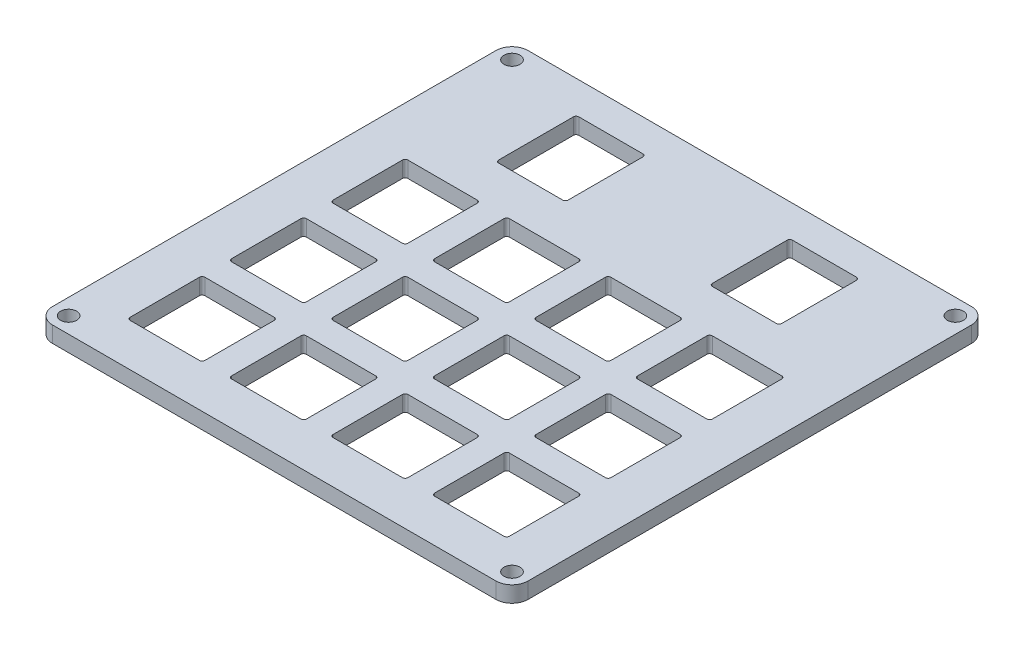
SolidWorks part; units mm, degrees
ref_plane "Front Plane" through (0, 0, 0) normal (0, 0, 1) x (1, 0, 0)
ref_plane "Top Plane" through (0, 0, 0) normal (0, 1, 0) x (1, 0, 0)
ref_plane "Right Plane" through (0, 0, 0) normal (1, 0, 0) x (0, 0, -1)
sketch "Sketch1" plane through (0, 0, 0) normal (0, 1, 0) x (1, 0, 0)
  line L0 (0, 0) -> (0, 50000) construction
  line L1 (-41.5, -44.5) -> (41.5, -44.5)
  line L3 (-41.5, 44.5) -> (41.5, 44.5)
  line L4 (44.5, -41.5) -> (44.5, 41.5)
  line L5 (-44.5, -44.5) -> (44.5, 44.5) construction
  line L6 (-44.5, 44.5) -> (44.5, -44.5) construction
  line L7 (0, 0) -> (50000, 0) construction
  line L19 (26, 23.5) -> (14, 23.5)
  line L20 (-29.9303, 29.9303) -> (38.5, -38.5) construction
  line L26 (-44.5, -41.5) -> (-44.5, 41.5)
  line L32 (-16.5, -36) -> (-16.5, -23)
  line L33 (-35, -36.5) -> (-22, -36.5)
  line L34 (-35.5, -36) -> (-35.5, -23)
  line L35 (-35, -22.5) -> (-22, -22.5)
  line L36 (-21.5, -36) -> (-21.5, -23)
  line L37 (-16, -36.5) -> (-3, -36.5)
  line L38 (-2.5, -36) -> (-2.5, -23)
  line L39 (-16, -22.5) -> (-3, -22.5)
  line L40 (2.5, -36) -> (2.5, -23)
  line L41 (3, -36.5) -> (16, -36.5)
  line L42 (16.5, -36) -> (16.5, -23)
  line L43 (3, -22.5) -> (16, -22.5)
  line L44 (21.5, -36) -> (21.5, -23)
  line L45 (22, -36.5) -> (35, -36.5)
  line L46 (35.5, -36) -> (35.5, -23)
  line L47 (22, -22.5) -> (35, -22.5)
  line L48 (-16.5, -17) -> (-16.5, -4)
  line L49 (-16, -17.5) -> (-3, -17.5)
  line L50 (-2.5, -17) -> (-2.5, -4)
  line L51 (-16, -3.5) -> (-3, -3.5)
  line L52 (2.5, -17) -> (2.5, -4)
  line L53 (3, -17.5) -> (16, -17.5)
  line L54 (16.5, -17) -> (16.5, -4)
  line L55 (3, -3.5) -> (16, -3.5)
  line L56 (21.5, -17) -> (21.5, -4)
  line L57 (22, -17.5) -> (35, -17.5)
  line L58 (35.5, -17) -> (35.5, -4)
  line L59 (22, -3.5) -> (35, -3.5)
  line L60 (-16.5, 2) -> (-16.5, 15)
  line L61 (-16, 1.5) -> (-3, 1.5)
  line L62 (-2.5, 2) -> (-2.5, 15)
  line L63 (-16, 15.5) -> (-3, 15.5)
  line L64 (2.5, 2) -> (2.5, 15)
  line L65 (3, 1.5) -> (16, 1.5)
  line L66 (16.5, 2) -> (16.5, 15)
  line L67 (3, 15.5) -> (16, 15.5)
  line L68 (21.5, 2) -> (21.5, 15)
  line L69 (22, 1.5) -> (35, 1.5)
  line L70 (35.5, 2) -> (35.5, 15)
  line L71 (22, 15.5) -> (35, 15.5)
  line L72 (-35.5, -17) -> (-35.5, -4)
  line L73 (-35, -17.5) -> (-22, -17.5)
  line L74 (-21.5, -17) -> (-21.5, -4)
  line L75 (-35, -3.5) -> (-22, -3.5)
  line L76 (-35.5, 2) -> (-35.5, 15)
  line L77 (-35, 1.5) -> (-22, 1.5)
  line L78 (-21.5, 2) -> (-21.5, 15)
  line L79 (-35, 15.5) -> (-22, 15.5)
  line L80 (-26, 38.5) -> (-14, 38.5)
  line L81 (-26.5, 38) -> (-26.5, 24)
  line L82 (-26, 23.5) -> (-14, 23.5)
  line L83 (-13.5, 38) -> (-13.5, 24)
  line L84 (13.5, 38) -> (13.5, 24)
  line L85 (26, 38.5) -> (14, 38.5)
  line L86 (26.5, 38) -> (26.5, 24)
  arc A0 (-41.5, -44.5) -> (-44.5, -41.5) centre (-41.5, -41.5) cw
  arc A1 (41.5, -44.5) -> (44.5, -41.5) centre (41.5, -41.5) ccw
  arc A2 (41.5, 44.5) -> (44.5, 41.5) centre (41.5, 41.5) cw
  arc A3 (-44.5, 41.5) -> (-41.5, 44.5) centre (-41.5, 41.5) cw
  circle A4 centre (-41.5, 41.5) radius 1.5
  circle A5 centre (41.5, 41.5) radius 1.5
  circle A8 centre (41.5, -41.5) radius 1.5
  circle A9 centre (-41.5, -41.5) radius 1.5
  arc A11 (-22, -36.5) -> (-21.5, -36) centre (-22, -36) ccw
  arc A12 (-22, -22.5) -> (-21.5, -23) centre (-22, -23) cw
  arc A13 (-35.5, -23) -> (-35, -22.5) centre (-35, -23) cw
  arc A14 (-35, -36.5) -> (-35.5, -36) centre (-35, -36) cw
  arc A15 (-16, -36.5) -> (-16.5, -36) centre (-16, -36) cw
  arc A16 (-16.5, -23) -> (-16, -22.5) centre (-16, -23) cw
  arc A17 (-3, -36.5) -> (-2.5, -36) centre (-3, -36) ccw
  arc A18 (-3, -22.5) -> (-2.5, -23) centre (-3, -23) cw
  arc A19 (3, -36.5) -> (2.5, -36) centre (3, -36) cw
  arc A20 (2.5, -23) -> (3, -22.5) centre (3, -23) cw
  arc A21 (16, -36.5) -> (16.5, -36) centre (16, -36) ccw
  arc A22 (16, -22.5) -> (16.5, -23) centre (16, -23) cw
  arc A23 (22, -36.5) -> (21.5, -36) centre (22, -36) cw
  arc A24 (21.5, -23) -> (22, -22.5) centre (22, -23) cw
  arc A25 (35, -36.5) -> (35.5, -36) centre (35, -36) ccw
  arc A26 (35, -22.5) -> (35.5, -23) centre (35, -23) cw
  arc A27 (-16, -17.5) -> (-16.5, -17) centre (-16, -17) cw
  arc A28 (-16.5, -4) -> (-16, -3.5) centre (-16, -4) cw
  arc A29 (-3, -17.5) -> (-2.5, -17) centre (-3, -17) ccw
  arc A30 (-3, -3.5) -> (-2.5, -4) centre (-3, -4) cw
  arc A31 (3, -17.5) -> (2.5, -17) centre (3, -17) cw
  arc A32 (2.5, -4) -> (3, -3.5) centre (3, -4) cw
  arc A33 (16, -17.5) -> (16.5, -17) centre (16, -17) ccw
  arc A34 (16, -3.5) -> (16.5, -4) centre (16, -4) cw
  arc A35 (22, -17.5) -> (21.5, -17) centre (22, -17) cw
  arc A36 (21.5, -4) -> (22, -3.5) centre (22, -4) cw
  arc A37 (35, -17.5) -> (35.5, -17) centre (35, -17) ccw
  arc A38 (35, -3.5) -> (35.5, -4) centre (35, -4) cw
  arc A39 (-16, 1.5) -> (-16.5, 2) centre (-16, 2) cw
  arc A40 (-16.5, 15) -> (-16, 15.5) centre (-16, 15) cw
  arc A41 (-3, 1.5) -> (-2.5, 2) centre (-3, 2) ccw
  arc A42 (-3, 15.5) -> (-2.5, 15) centre (-3, 15) cw
  arc A43 (3, 1.5) -> (2.5, 2) centre (3, 2) cw
  arc A44 (2.5, 15) -> (3, 15.5) centre (3, 15) cw
  arc A45 (16, 1.5) -> (16.5, 2) centre (16, 2) ccw
  arc A46 (16, 15.5) -> (16.5, 15) centre (16, 15) cw
  arc A47 (22, 1.5) -> (21.5, 2) centre (22, 2) cw
  arc A48 (21.5, 15) -> (22, 15.5) centre (22, 15) cw
  arc A49 (35, 1.5) -> (35.5, 2) centre (35, 2) ccw
  arc A50 (35, 15.5) -> (35.5, 15) centre (35, 15) cw
  arc A51 (-35, -17.5) -> (-35.5, -17) centre (-35, -17) cw
  arc A52 (-35.5, -4) -> (-35, -3.5) centre (-35, -4) cw
  arc A53 (-22, -17.5) -> (-21.5, -17) centre (-22, -17) ccw
  arc A54 (-22, -3.5) -> (-21.5, -4) centre (-22, -4) cw
  arc A55 (-35, 1.5) -> (-35.5, 2) centre (-35, 2) cw
  arc A56 (-35.5, 15) -> (-35, 15.5) centre (-35, 15) cw
  arc A57 (-22, 1.5) -> (-21.5, 2) centre (-22, 2) ccw
  arc A58 (-22, 15.5) -> (-21.5, 15) centre (-22, 15) cw
  arc A59 (-14, 23.5) -> (-13.5, 24) centre (-14, 24) ccw
  arc A60 (-14, 38.5) -> (-13.5, 38) centre (-14, 38) cw
  arc A61 (-26, 38.5) -> (-26.5, 38) centre (-26, 38) ccw
  arc A62 (-26.5, 24) -> (-26, 23.5) centre (-26, 24) ccw
  arc A63 (14, 23.5) -> (13.5, 24) centre (14, 24) cw
  arc A64 (14, 38.5) -> (13.5, 38) centre (14, 38) ccw
  arc A65 (26, 38.5) -> (26.5, 38) centre (26, 38) cw
  arc A66 (26.5, 24) -> (26, 23.5) centre (26, 24) cw
  point P0 (0, 0)
  point P26 (0, 0)
  point P31 (0, 0)
  point P44 (-21.5, -36.5)
  point P47 (-21.5, -22.5)
  point P50 (-35.5, -22.5)
  point P53 (-35.5, -36.5)
  point P54 (-28.5, -22.5)
  point P55 (-13.5, 38.5)
  point P190 (-26.5, 38.5)
  point P193 (-26.5, 23.5)
  dimension "D3" = 3
  dimension "D4" = 3
  dimension "D6" = 9
  dimension "D7" = 13
  dimension "D14" = 0.5
  dimension "D12" = 6
  dimension "D20" = 0.5
  dimension "D1" = 89
  dimension "D2" = 89
  dimension "D5" = 8
  dimension "D8" = 15
  dimension "D9" = 89
  dimension "D10" = 14
  dimension "D11" = 14
  dimension "D13" = 89
  dimension "D17" = 5
  dimension "D18" = 5
  dimension "D19" = 18
  dimension "D15" = 4
  dimension "D16" = 3
extrude "Boss-Extrude1" add sketch "Sketch1" along normal blind 3
